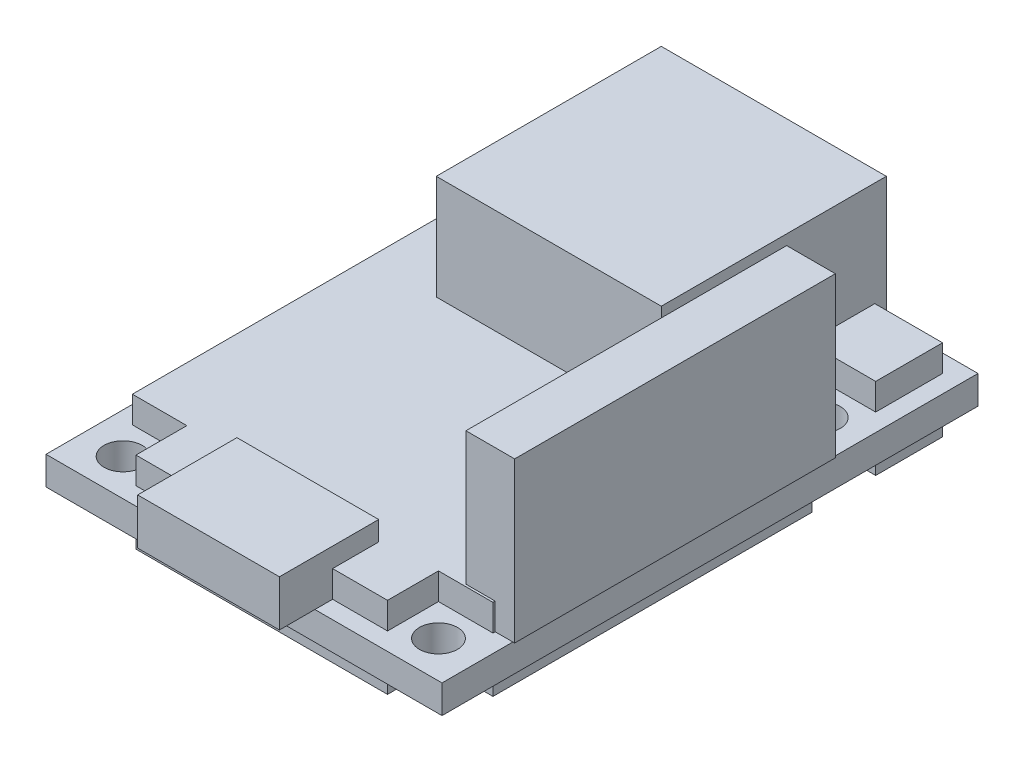
SolidWorks part; units mm, degrees
ref_plane "Front Plane" through (0, 0, 0) normal (0, 0, 1) x (1, 0, 0)
ref_plane "Top Plane" through (0, 0, 0) normal (0, 1, 0) x (1, 0, 0)
ref_plane "Right Plane" through (0, 0, 0) normal (1, 0, 0) x (0, 0, -1)
sketch "Sketch1" plane through (0, 0, 0) normal (0, 1, 0) x (1, 0, 0)
  line L1 (-11.175, -15.125) -> (11.175, -15.125)
  line L2 (-11.175, -15.125) -> (-11.175, 15.125)
  line L3 (-11.175, 15.125) -> (11.175, 15.125)
  line L4 (11.175, -15.125) -> (11.175, 15.125)
  line L5 (-11.175, -15.125) -> (11.175, 15.125) construction
  line L6 (-11.175, 15.125) -> (11.175, -15.125) construction
  point P0 (0, 0)
  dimension "D1" = 30.25
  dimension "D2" = 22.35
extrude "Boss-Extrude1" add sketch "Sketch1" along normal mid plane 1.6
sketch "Sketch2" plane through (0, 0, 0) normal (0, 1, 0) x (1, 0, 0)
  line L0 (8.9, 9.625) -> (8.9, 15.125) construction
  line L1 (11.175, 15.125) -> (-11.175, 15.125) construction
  line L2 (8.9, 7.475) -> (8.9, -11.975) construction
  line L3 (8.9, -14.125) -> (8.9, -15.125) construction
  line L4 (-11.175, -15.125) -> (11.175, -15.125) construction
  line L5 (9.975, 8.55) -> (11.175, 8.55) construction
  line L6 (11.175, -15.125) -> (11.175, 15.125) construction
  line L7 (7.825, 8.55) -> (-11.175, 8.55) construction
  line L8 (-11.175, 15.125) -> (-11.175, -15.125) construction
  line L9 (0, 15.125) -> (0, -15.125) construction
  circle A0 centre (8.9, 8.55) radius 1.075
  circle A1 centre (8.9, -13.05) radius 1.075
  circle A2 centre (-8.9, 8.55) radius 1.075
  circle A3 centre (-8.9, -13.05) radius 1.075
  dimension "D2" = 2.15
  dimension "D1" = 1.2
  dimension "D3" = 5.5
  dimension "D4" = 1
extrude "Cut-Extrude1" cut sketch "Sketch2" against normal through all both and the other way through all
sketch "Sketch3" plane through (0, 0, 0) normal (0, 1, 0) x (1, 0, 0)
  line L0 (-10.175, 6.75) -> (-7.1, 6.75)
  line L1 (-7.1, 6.75) -> (-7.1, 10.35)
  line L2 (-7.1, 10.35) -> (-10.175, 10.35)
  line L3 (-10.175, 10.35) -> (-10.175, 14.125)
  line L4 (-10.175, 14.125) -> (10.175, 14.125)
  line L5 (-10.175, 6.75) -> (-10.175, -2.25)
  line L6 (-8.9, 8.55) -> (8.9, -13.05) construction
  line L7 (0, -2.25) -> (0, 14.125) construction
  line L8 (0, -2.25) -> (-10.175, -2.25) construction
  line L9 (-8.9, 10.35) -> (-8.9, 8.55) construction
  line L10 (-8.9, 8.55) -> (-8.9, 6.75) construction
  line L11 (-8.9, 8.55) -> (-7.1, 8.55) construction
  line L12 (-4.8043, 14.125) -> (-4.8043, 15.125) construction
  line L13 (11.175, 15.125) -> (-11.175, 15.125) construction
  line L14 (-10.175, 2.25) -> (-11.175, 2.25) construction
  line L15 (-11.175, 15.125) -> (-11.175, -15.125) construction
  line L16 (-10.175, -2.25) -> (-10.175, -11.25)
  line L17 (-10.175, -11.25) -> (-7.1, -11.25)
  line L18 (-7.1, -11.25) -> (-7.1, -14.125)
  line L19 (-7.1, -14.125) -> (7.1, -14.125)
  line L20 (0, -2.25) -> (0, -14.125) construction
  line L22 (-3.0515, -14.125) -> (-3.0515, -15.125) construction
  line L23 (-11.175, -15.125) -> (11.175, -15.125) construction
  line L24 (-8.9, -13.05) -> (-8.9, -11.25) construction
  line L25 (-8.9, -11.25) -> (-8.9, -13.05) construction
  line L26 (-8.9, -13.05) -> (-7.1, -13.05) construction
  line L27 (10.175, 10.35) -> (10.175, 14.125)
  line L28 (7.1, 10.35) -> (10.175, 10.35)
  line L29 (7.1, 6.75) -> (7.1, 10.35)
  line L30 (10.175, 6.75) -> (7.1, 6.75)
  line L31 (10.175, 6.75) -> (10.175, -2.25)
  line L32 (10.175, -2.25) -> (10.175, -11.25)
  line L33 (10.175, -11.25) -> (7.1, -11.25)
  line L34 (7.1, -11.25) -> (7.1, -14.125)
  dimension "D1" = 1.8
  dimension "D2" = 1
extrude "Boss-Extrude2" add sketch "Sketch3" along normal mid plane 4.6
sketch "Sketch4" plane through (0, 0.8, 0) normal (0, 1, 0) x (1, 0, 0)
  line L0 (0, -14.325) -> (0, 0) construction
  line L1 (4, -17.125) -> (-4, -17.125)
  line L2 (4, -17.125) -> (4, -11.525)
  line L3 (4, -11.525) -> (-4, -11.525)
  line L4 (-4, -17.125) -> (-4, -11.525)
  line L5 (4, -17.125) -> (-4, -11.525) construction
  line L6 (4, -11.525) -> (-4, -17.125) construction
  line L7 (-11.175, -15.125) -> (11.175, -15.125) construction
  point P0 (0, -14.325)
  dimension "D1" = 5.6
  dimension "D2" = 8
  dimension "D3" = 2
extrude "Boss-Extrude3" add sketch "Sketch4" along normal blind 2.6
sketch "Sketch5" plane through (0, 0.8, 0) normal (0, 1, 0) x (1, 0, 0)
  line L0 (11.175, 15.125) -> (-11.175, 15.125) construction
  line L1 (-6.35, 14.775) -> (6.35, 14.775)
  line L2 (-6.35, 14.775) -> (-6.35, 2.075)
  line L3 (-6.35, 2.075) -> (6.35, 2.075)
  line L4 (6.35, 14.775) -> (6.35, 2.075)
  line L5 (-6.35, 14.775) -> (6.35, 2.075) construction
  line L6 (-6.35, 2.075) -> (6.35, 14.775) construction
  line L7 (0, 0) -> (0, 8.425) construction
  point P0 (0, 8.425)
  dimension "D1" = 6.7
  dimension "D2" = 12.7
  dimension "D3" = 12.7
extrude "Boss-Extrude4" add sketch "Sketch5" along normal blind 7.4
sketch "Sketch6" plane through (0, 0.8, 0) normal (0, 1, 0) x (1, 0, 0)
  line L0 (11.275, 6.975) -> (8.525, 6.975)
  line L1 (11.275, 6.975) -> (11.275, -11.125)
  line L2 (8.525, 6.975) -> (8.525, -11.125)
  line L3 (11.275, -11.125) -> (8.525, -11.125)
  line L4 (11.175, 15.125) -> (-11.175, 15.125) construction
  line L5 (4, -15.125) -> (11.175, -15.125) construction
  line L6 (11.175, -15.125) -> (11.175, 15.125) construction
  dimension "D1" = 8.15
  dimension "D2" = 4
  dimension "D3" = 0.1
  dimension "D4" = 2.65
extrude "Boss-Extrude5" add sketch "Sketch6" along normal blind 9
